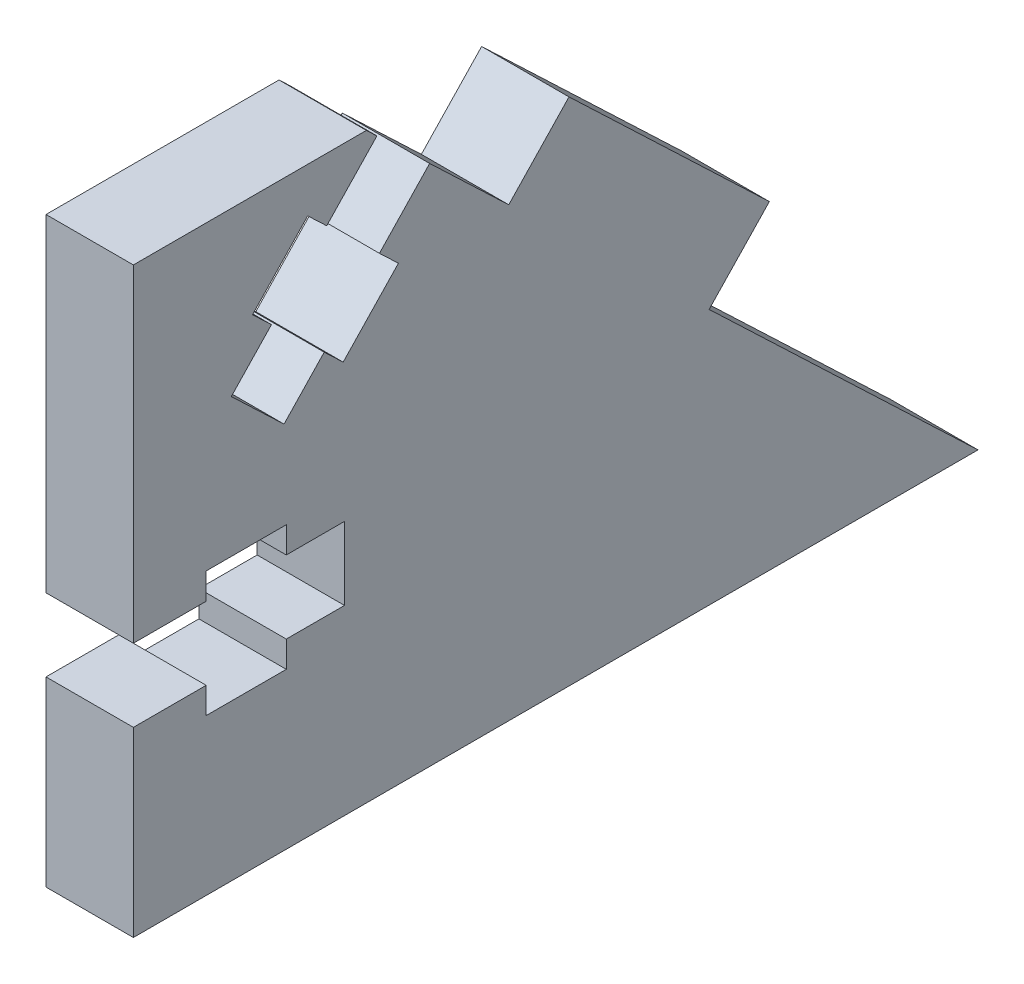
SolidWorks part; units mm, degrees
ref_plane "Plan de face" through (0, 0, 0) normal (0, 0, 1) x (1, 0, 0)
ref_plane "Plan de dessus" through (0, 0, 0) normal (0, 1, 0) x (1, 0, 0)
ref_plane "Plan de droite" through (0, 0, 0) normal (1, 0, 0) x (0, 0, -1)
sketch "Esquisse1" plane through (0, 0, 0) normal (1, 0, 0) x (0, 0, -1)
  line L0 (0, 0) -> (0, 40)
  line L1 (0, 40) -> (16, 40)
  line L2 (16, 40) -> (25.7759, 30.6897)
  line L3 (58, 0) -> (0, 0)
  line L4 (25.7759, 30.6897) -> (29.9138, 35.0345)
  line L5 (29.9138, 35.0345) -> (43.6724, 21.931)
  line L6 (43.6724, 21.931) -> (39.5345, 17.5862)
  line L7 (39.5345, 17.5862) -> (58, 0)
  dimension "D1" = 40
  dimension "D2" = 16
  dimension "D3" = 58
  dimension "D4" = 13.5
  dimension "D5" = 19
  dimension "D6" = 6
extrude "Boss.-Extru.1" add sketch "Esquisse1" along normal blind 6
sketch "Esquisse2" plane through (6, 0, 0) normal (1, 0, 0) x (0, 0, -1)
  line L0 (0, 40) -> (0, 0) construction
  line L1 (25.7759, 30.6897) -> (16, 40) construction
  line B0 (0, -0.5) -> (-5, -0.5)
  line B1 (-6, 0.5) -> (-6, 6.5)
  line B2 (-5, 7.5) -> (0, 7.5)
  line B3 (0, 7.5) -> (0, 12.5)
  line B4 (0, 12.5) -> (5, 12.5)
  line B5 (5, 12.5) -> (5, 10.7)
  line B6 (5, 10.7) -> (10.5, 10.7)
  line B7 (10.5, 10.7) -> (10.5, 12.5)
  line B8 (10.5, 12.5) -> (14.5, 12.5)
  line B9 (14.5, 12.5) -> (14.5, 17.5)
  line B10 (14.5, 15) -> (0, 15) construction
  line B11 (0, 30.5) -> (0, 22.5)
  line B12 (0, 7.5) -> (0, -0.5)
  line B13 (10.5, 17.5) -> (14.5, 17.5)
  line B14 (10.5, 19.3) -> (10.5, 17.5)
  line B15 (5, 19.3) -> (10.5, 19.3)
  line B16 (5, 17.5) -> (5, 19.3)
  line B17 (0, 17.5) -> (5, 17.5)
  line B18 (0, 22.5) -> (0, 17.5)
  line B19 (-5, 22.5) -> (0, 22.5)
  line B20 (-6, 29.5) -> (-6, 23.5)
  line B21 (0, 30.5) -> (-5, 30.5)
  line B22 (0, 12.5) -> (0, 17.5)
  arc B23 (-6, 6.5) -> (-5, 7.5) centre (-5, 6.5) cw
  arc B24 (-5, -0.5) -> (-6, 0.5) centre (-5, 0.5) cw
  arc B25 (-5, 30.5) -> (-6, 29.5) centre (-5, 29.5) ccw
  arc B26 (-6, 23.5) -> (-5, 22.5) centre (-5, 23.5) ccw
  line B27 (7.3103, 48.2759) -> (10.7586, 51.8966)
  line B28 (12.1724, 51.931) -> (16.5172, 47.7931)
  line B29 (16.5517, 46.3793) -> (13.1034, 42.7586)
  line B30 (13.1034, 42.7586) -> (16.7241, 39.3103)
  line B31 (16.7241, 39.3103) -> (13.2759, 35.6897)
  line B32 (13.2759, 35.6897) -> (11.9724, 36.931)
  line B33 (11.9724, 36.931) -> (8.1793, 32.9483)
  line B34 (8.1793, 32.9483) -> (9.4828, 31.7069)
  line B35 (9.4828, 31.7069) -> (6.7241, 28.8103)
  line B36 (6.7241, 28.8103) -> (10.3448, 25.3621)
  line B37 (8.5345, 27.0862) -> (18.5345, 37.5862) construction
  line B38 (29.7586, 26.8966) -> (23.9655, 32.4138)
  line B39 (13.1034, 42.7586) -> (7.3103, 48.2759)
  line B40 (13.1034, 28.2586) -> (10.3448, 25.3621)
  line B41 (14.4069, 27.0172) -> (13.1034, 28.2586)
  line B42 (18.2, 31) -> (14.4069, 27.0172)
  line B43 (16.8966, 32.2414) -> (18.2, 31)
  line B44 (20.3448, 35.8621) -> (16.8966, 32.2414)
  line B45 (23.9655, 32.4138) -> (20.3448, 35.8621)
  line B46 (27.4138, 36.0345) -> (23.9655, 32.4138)
  line B47 (33.1724, 31.931) -> (28.8276, 36.069)
  line B48 (29.7586, 26.8966) -> (33.2069, 30.5172)
  line B49 (16.7241, 39.3103) -> (20.3448, 35.8621)
  arc B50 (16.5172, 47.7931) -> (16.5517, 46.3793) centre (15.8276, 47.069) cw
  arc B51 (10.7586, 51.8966) -> (12.1724, 51.931) centre (11.4828, 51.2069) cw
  arc B52 (33.2069, 30.5172) -> (33.1724, 31.931) centre (32.4828, 31.2069) ccw
  arc B53 (28.8276, 36.069) -> (27.4138, 36.0345) centre (28.1379, 35.3448) ccw
  line M2 (25.7759, 30.6897) -> (16, 40)
  line M4 (0, 40) -> (0, 0)
  dimension "D1" = 15
  dimension "D2" = 1
sketch_block_instance "attache_male-1"
sketch_block "attache_male" parameters "D7"=1, "D1"=5, "D2"=5, "D3"=5.5, "D4"=1.8, "D5"=4, "D6"=2.5
sketch_block_instance "attache_male-2"
extrude "Enlèv. mat.-Extru.1" cut sketch "Esquisse2" against normal blind 6 contours B17 B4 B5 B6 B7 B8 B9 B13 B14 B15 B16 M4 | B44 B31 B32 B33 B34 B35 B36 B40 B41 B42 B43 M2
sketch "Esquisse3" [suppressed] plane through (6, 0, 0) normal (1, 0, 0) x (0, 0, -1)
  line L0 (25.7759, 30.6897) -> (20.3448, 35.8621) construction
  line L1 (18.1621, 29.6552) -> (38.4379, 10.3448)
  line L2 (18.1621, 29.6552) -> (14.0241, 25.3103)
  line L3 (14.0241, 25.3103) -> (34.3, 6)
  line L4 (38.4379, 10.3448) -> (34.3, 6)
  line L5 (18.1621, 29.6552) -> (34.3, 6) construction
  line L6 (14.0241, 25.3103) -> (38.4379, 10.3448) construction
  line L7 (0, 0) -> (58, 0) construction
  point P0 (26.231, 17.8276)
  dimension "D1" = 6
  dimension "D2" = 28
  dimension "D3" = 6
  dimension "D4" = 6
extrude "Enlèv. mat.-Extru.2" [suppressed] cut sketch "Esquisse3" against normal blind 6
